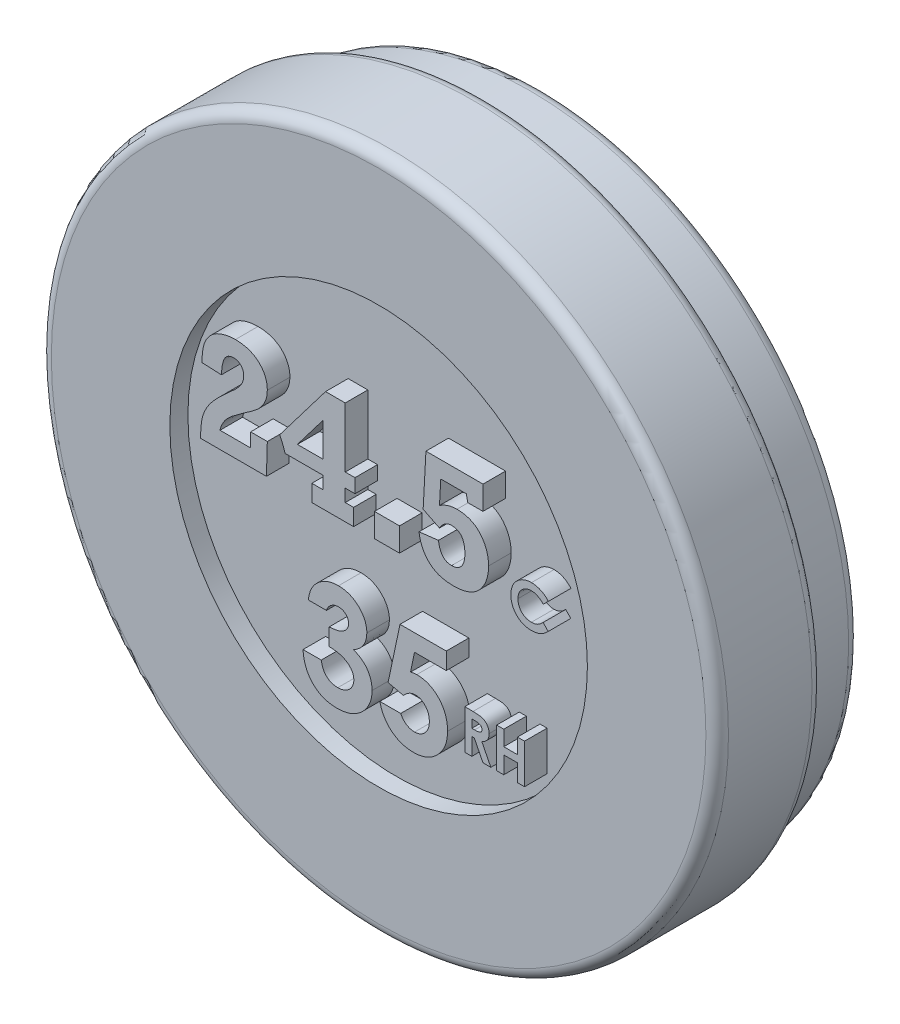
SolidWorks part; units mm, degrees
ref_plane "Front Plane" through (0, 0, 0) normal (0, 0, 1) x (1, 0, 0)
ref_plane "Top Plane" through (0, 0, 0) normal (0, 1, 0) x (1, 0, 0)
ref_plane "Right Plane" through (0, 0, 0) normal (1, 0, 0) x (0, 0, -1)
sketch "Sketch1" plane through (0, 0, 0) normal (0, 0, 1) x (1, 0, 0)
  circle A0 centre (0, 0) radius 30
  dimension "D1" = 60
extrude "Boss-Extrude1" add sketch "Sketch1" along normal blind 14.4
sketch "Sketch2" plane through (0, 0, 0) normal (0, 0, -1) x (-1, 0, 0)
  circle A0 centre (0, 0) radius 28.25
  dimension "D1" = 56.5
extrude "Cut-Extrude1" cut sketch "Sketch2" against normal blind 5 flip side to cut
fillet "Fillet1" radius 1 3 edges at (-30, 0, 5) (-28.25, 0, 0) (30, 0, 14.4)
sketch "Sketch3" plane through (0, 0, 14.4) normal (0, 0, 1) x (1, 0, 0)
  circle A0 centre (0, 0) radius 18.5
  dimension "D1" = 37
extrude "Cut-Extrude2" cut sketch "Sketch3" against normal blind 1.6
sketch "Sketch4" plane through (0, 0, 12.8) normal (0, 0, 1) x (1, 0, 0)
  text T0 "24.5" font "Rockwell" height 9
  text T1 "<b>C</b>"
  text T2 "<b>RH</b>"
  text T3 "<b>35</b>" font "Century Gothic" height 9
sketch "Sketch5" plane through (0, 0, 0) normal (0, 0, -1) x (-1, 0, 0)
  line L0 (-20.8204, 3.5) -> (11.274, 3.5) construction
  line L1 (11.274, 3.5) -> (25.5063, 3.5) construction
  line L2 (-24.977, 0) -> (25.5063, 0) construction
  circle A0 centre (-18, 0) radius 2.75
  circle A1 centre (18, 0) radius 2.75
  text T0 "C/F" font "Century Gothic" height 2.5
  text T1 "<b>ON/OFF</b>" font "Century Gothic" height 2.5
  point P1 (-20.2734, 3.5492)
  point P10 (25.5063, 2.8348)
  point P11 (8.8193, 3.4169)
  point P12 (10.3587, 3.5833)
  point P13 (11.274, 3.5833)
  point P14 (-23.257, 3.7481)
  point P15 (10.9555, 3.5833)
  point P16 (0, 0)
  point P17 (-16.2454, 0)
  point P18 (0, 0)
  point P19 (-20.8204, 3.4497)
  dimension "D3" = 5.5
  dimension "D1" = 18
  dimension "D2" = 18
  dimension "D4" = 3.5
extrude "Boss-Extrude2" add sketch "Sketch5" along normal blind 2
extrude "Boss-Extrude3" add sketch "Sketch4" along normal blind 2
sketch "Sketch6" plane through (0, 0, 0) normal (0, 0, -1) x (-1, 0, 0)
  line L0 (0, 0) -> (0, -25.2247) construction
  line L1 (0, 0) -> (0, 25.0607) construction
  line L2 (0, -17.75) -> (10.254, -17.75) construction
  line L3 (0, 25) -> (7.875, 25) construction
  line L4 (0, -28.25) -> (20.5863, -28.25) construction
  circle A0 centre (0, 17.5) radius 7.5
  circle A1 centre (0, -5.25) radius 12.5
  circle A3 centre (0, 0) radius 27.25 construction
  circle A4 centre (0, 0) radius 28.25 construction
  circle A5 centre (0, 0) radius 28.25 construction
  circle A6 centre (0, 17.5) radius 7.3
  circle A7 centre (0, -5.25) radius 12.3
  point P18 (0, -28.25)
  point P21 (0, -5.25)
  point P22 (0, -28.25)
  dimension "D1" = 25
  dimension "D3" = 15
  dimension "D2" = 17.75
  dimension "D4" = 25
  dimension "D5" = 10.5
  dimension "D6" = 0.2
extrude "Cut-Extrude3" cut sketch "Sketch6" against normal blind 1
sketch "Sketch7" plane through (0, 0, 0) normal (0, 0, -1) x (-1, 0, 0)
  line L0 (0, 0) -> (0, -28) construction
  line L1 (-10.3, -19.85) -> (10.3, -19.85)
  line L2 (-10.3, -19.85) -> (-10.3, -22.1)
  line L3 (-10.3, -22.1) -> (10.3, -22.1)
  line L4 (10.3, -19.85) -> (10.3, -22.1)
  line L5 (-10.3, -19.85) -> (10.3, -22.1) construction
  line L6 (-10.3, -22.1) -> (10.3, -19.85) construction
  line L7 (0, -28) -> (2.5979, -28) construction
  point P4 (0, -20.975)
  dimension "D1" = 2.25
  dimension "D2" = 20.6
  dimension "D3" = 28
  dimension "D4" = 5.9
extrude "Cut-Extrude4" cut sketch "Sketch7" against normal blind 4
